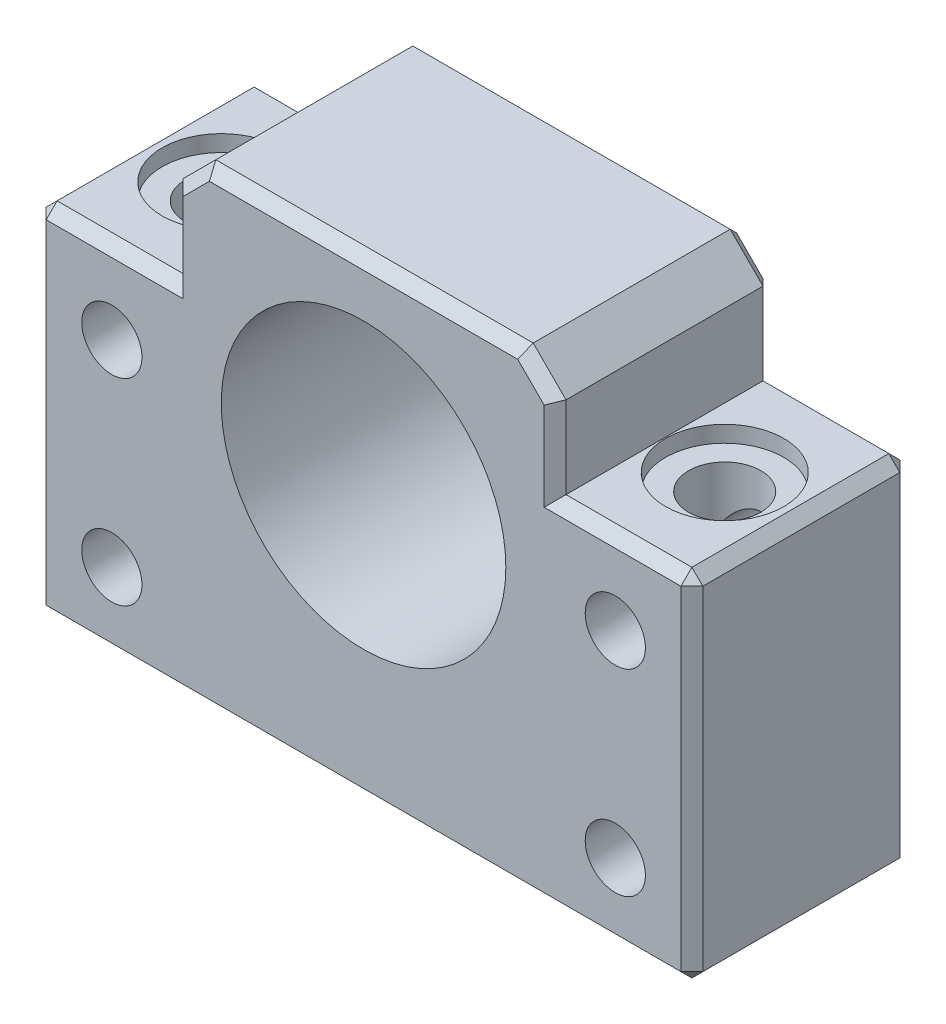
SolidWorks part; units mm, degrees
material "Liga 6061"
ref_plane "Plano frontal" through (0, 0, 0) normal (0, 0, 1) x (1, 0, 0)
ref_plane "Plano superior" through (0, 0, 0) normal (0, 1, 0) x (1, 0, 0)
ref_plane "Plano direito" through (0, 0, 0) normal (1, 0, 0) x (0, 0, -1)
sketch "Esboço1" plane through (0, 0, 0) normal (0, 0, 1) x (1, 0, 0)
  line L0 (-30, -25) -> (-30, 7.5)
  line L1 (-30, 7.5) -> (-17.5, 7.5)
  line L2 (-17.5, 7.5) -> (-17.5, 18)
  line L4 (-17.5, 18) -> (17.5, 18)
  line L6 (17.5, 18) -> (17.5, 7.5)
  line L7 (17.5, 7.5) -> (30, 7.5)
  line L8 (30, 7.5) -> (30, -25)
  line L9 (30, -25) -> (-30, -25)
  circle A0 centre (0, 0) radius 13
  point P5 (0, -25)
  point P7 (0, 18)
  dimension "D2" = 26
  dimension "D1" = 60
  dimension "D3" = 35
  dimension "D4" = 25
  dimension "D5" = 32.5
  dimension "D6" = 43
extrude "Ressalto-extrusão1" add sketch "Esboço1" along normal blind 20
sketch "Esboço4" plane through (0, 7.5, 0) normal (0, 1, 0) x (1, 0, 0)
  line L0 (-30, -20) -> (-30, 0) construction
  line L1 (30, -20) -> (30, 0) construction
  circle A0 centre (-23, -10) radius 3.3
  circle A1 centre (23, -10) radius 3.3
  point P4 (-30, -10)
  dimension "D3" = 6.6
  dimension "D1" = 7
  dimension "D2" = 7
extrude "Corte-extrusão1" cut sketch "Esboço4" against normal through all
chamfer "Chanfro1" distance 3 angle 45 2 edges at (17.5, 18, 10) (-17.5, 18, 10)
chamfer "Chanfro3" distance 1 angle 45 24 edges at (30, -8.75, 0) (-30, -8.75, 0) (-23.75, 7.5, 0) (-17.5, 11.25, 0) (-16, 16.5, 0) (0, 18, 0) (16, 16.5, 0) (17.5, 11.25, 0) (23.75, 7.5, 0) (30, 7.5, 10) (16, 16.5, 20) (17.5, 11.25, 20) (23.75, 7.5, 20) (30, -8.75, 20) (0, -25, 20) (-30, -8.75, 20) (-23.75, 7.5, 20) (-17.5, 11.25, 20) (-16, 16.5, 20) (0, 18, 20) (-30, 7.5, 10) (30, -25, 10) (0, -25, 0) (-30, -25, 10)
sketch "Esboço5" plane through (0, 7.5, 0) normal (0, 1, 0) x (1, 0, 0)
  circle A0 centre (23, -10) radius 5.4
  circle A1 centre (-23, -10) radius 5.4
  dimension "D1" = 10.8
extrude "Corte-extrusão2" cut sketch "Esboço5" against normal blind 1.5 contours A0 | A1
sketch "Esboço6" plane through (0, 0, 0) normal (0, 0, -1) x (-1, 0, 0)
  line L0 (29, -25) -> (-29, -25) construction
  line L1 (-30, -24) -> (-30, 6.5) construction
  circle A0 centre (-23, 0) radius 2.75
  circle A1 centre (-23, -18) radius 2.75
  circle A2 centre (23, 0) radius 2.75
  circle A3 centre (23, -18) radius 2.75
  dimension "D3" = 5.5
  dimension "D1" = 25
  dimension "D2" = 18
  dimension "D4" = 7
  dimension "D5" = 46
extrude "Corte-extrusão3" cut sketch "Esboço6" against normal through all
